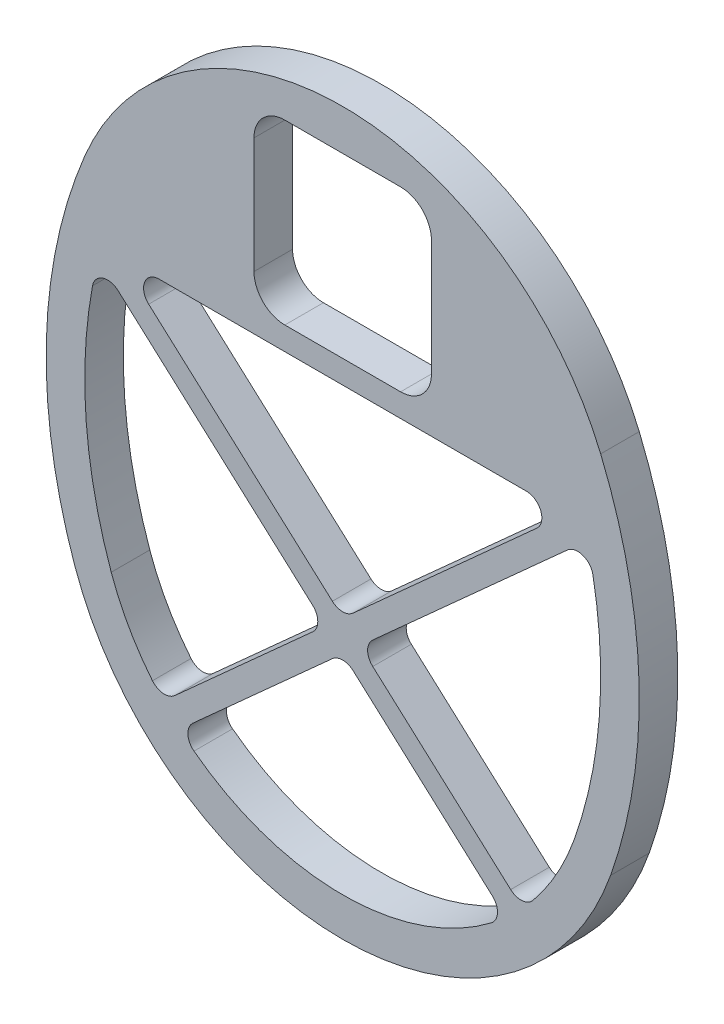
SolidWorks part; units mm, degrees
material "Balsa"
ref_plane "Front Plane" through (0, 0, 0) normal (0, 0, 1) x (1, 0, 0)
ref_plane "Top Plane" through (0, 0, 0) normal (0, 1, 0) x (1, 0, 0)
ref_plane "Right Plane" through (0, 0, 0) normal (1, 0, 0) x (0, 0, -1)
sketch "Sketch1" plane through (0, 0, 0) normal (0, 0, 1) x (1, 0, 0)
  line L8 (-38.1, 0) -> (38.1, 0) construction
  line L9 (-42.458, 57.15) -> (42.458, 57.15)
  line L10 (-38.1, 50.8) -> (38.1, 50.8)
  line L14 (-39.6987, 45.72) -> (39.6987, 45.72)
  line L21 (-44.0868, -2.1167) -> (-38.1, 0)
  line L22 (38.1, 0) -> (44.0868, -2.1167)
  arc A0 (38.1, 50.8) -> (38.1, 0) centre (-33.742, 25.4) cw
  arc A1 (-38.1, 50.8) -> (-38.1, 0) centre (33.742, 25.4) ccw
  arc A2 (-42.458, 57.15) -> (-44.0868, -2.1167) centre (33.742, 25.4) ccw
  arc A3 (42.458, 57.15) -> (44.0868, -2.1167) centre (-33.742, 25.4) cw
  arc A4 (-44.0868, 52.9167) -> (-44.0868, -2.1167) centre (33.742, 25.4) ccw construction
  arc A5 (44.0868, 52.9167) -> (44.0868, -2.1167) centre (-33.742, 25.4) cw construction
  arc A6 (38.1, 50.8) -> (38.1, 0) centre (-33.742, 25.4) cw construction
  arc A7 (-38.1, 50.8) -> (-38.1, 0) centre (33.742, 25.4) ccw construction
  arc A8 (-42.458, 57.15) -> (42.458, 57.15) centre (0, 39.4592) cw
  arc A9 (-38.1, 0) -> (38.1, 0) centre (0, 13.4704) ccw
  arc A10 (-44.0868, -2.1167) -> (44.0868, -2.1167) centre (0, 13.4704) ccw
  point P0 (0, 0)
  point P13 (0, 50.8)
  dimension "D7" = 76.2
  dimension "D2" = 76.2
  dimension "D8" = 5.08
  dimension "D3" = 50.8
  dimension "D6" = 76.2
  dimension "D1" = 6.35
  dimension "D4" = 6.35
  dimension "D5" = 6.35
extrude "Boss-Extrude1" add sketch "Sketch1" along normal blind 6.35
sketch "Sketch2" plane through (0, 0, 6.35) normal (0, 0, 1) x (1, 0, 0)
  line L0 (0, 45.72) -> (0, 85.4553) construction
  line L1 (-14.605, 78.74) -> (14.605, 78.74)
  line L2 (-14.605, 78.74) -> (-14.605, 49.53)
  line L3 (-14.605, 49.53) -> (14.605, 49.53)
  line L4 (14.605, 78.74) -> (14.605, 49.53)
  line L5 (-14.605, 78.74) -> (14.605, 49.53) construction
  line L6 (-14.605, 49.53) -> (14.605, 78.74) construction
  line L8 (-39.6987, 45.72) -> (39.6987, 45.72) construction
  arc A0 (42.458, 57.15) -> (-42.458, 57.15) centre (0, 39.4592) ccw construction
  point P0 (0, 64.135)
  dimension "D1" = 29.21
  dimension "D2" = 29.21
  dimension "D3" = 3.81
extrude "Cut-Extrude1" cut sketch "Sketch2" against normal up to next
fillet "Fillet1" radius 5.08 4 edges at (14.605, 49.53, 3.175) (14.605, 78.74, 3.175) (-14.605, 78.74, 3.175) (-14.605, 49.53, 3.175)
sketch "Sketch3" plane through (0, 0, 6.35) normal (0, 0, 1) x (1, 0, 0)
  line L0 (-40.9734, 44.3043) -> (-38.424, 47.1357)
  line L1 (-40.9734, 44.3043) -> (28.8674, -18.5806)
  line L2 (-38.424, 47.1357) -> (31.4168, -15.7492)
  line L3 (28.8674, -18.5806) -> (31.4168, -15.7492)
  line L4 (38.424, 47.1357) -> (40.9734, 44.3043)
  line L5 (38.424, 47.1357) -> (-31.4168, -15.7492)
  line L6 (40.9734, 44.3043) -> (-28.8674, -18.5806)
  line L7 (-31.4168, -15.7492) -> (-28.8674, -18.5806)
  line L8 (-39.6987, 45.72) -> (39.6987, 45.72) construction
  point P0 (39.6987, 45.72)
  point P7 (-39.6987, 45.72)
  line M18 (-39.6987, 45.72) -> (39.6987, 45.72)
  arc M19 (39.6987, 45.72) -> (38.1, 0) centre (-33.742, 25.4) cw
  arc M20 (38.1, 0) -> (-38.1, 0) centre (0, 13.4704) cw
  dimension "D1" = 3.81
  dimension "D2" = 3.81
  dimension "D3" = 42
  dimension "D4" = 42
  dimension "D5" = 93.98
  dimension "D6" = 93.98
extrude "Boss-Extrude2" add sketch "Sketch3" against normal up to surface (6.35 mm away) contours L6 L5 L2 M19 M18 | L6 L1 L5 M20 up to face at (0, 64.135, 0)
fillet "Fillet2" radius 2.54 12 edges at (2.847, 9.9752, 3.175) (40.2414, 43.6453, 3.175) (29.5636, -14.0806, 3.175) (-26.8316, -16.7476, 3.175) (0, 7.4117, 3.175) (26.8316, -16.7476, 3.175) (-2.847, 9.9752, 3.175) (-29.5636, -14.0806, 3.175) (-40.2414, 43.6453, 3.175) (36.8517, 45.72, 3.175) (-36.8517, 45.72, 3.175) (0, 12.5386, 3.175)
